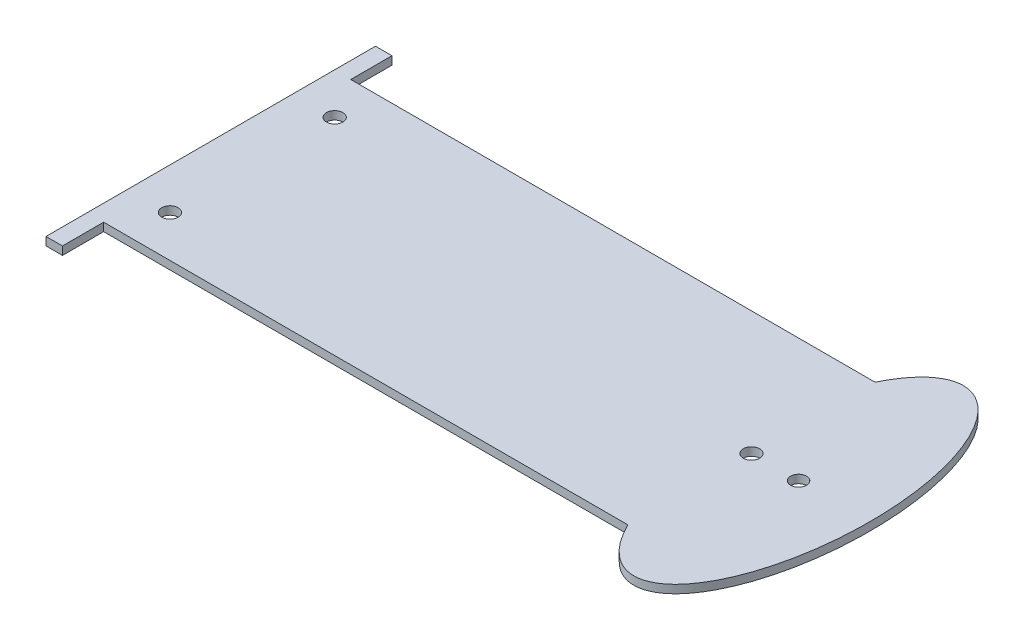
SolidWorks part; units mm, degrees
ref_plane "Front Plane" through (0, 0, 0) normal (0, 0, 1) x (1, 0, 0)
ref_plane "Top Plane" through (0, 0, 0) normal (0, 1, 0) x (1, 0, 0)
ref_plane "Right Plane" through (0, 0, 0) normal (1, 0, 0) x (0, 0, -1)
sketch "Sketch1" plane through (0, 0, 0) normal (0, 1, 0) x (1, 0, 0)
  line L0 (107.6735, 26.1875) -> (108.6754, 26.1875)
  line L1 (-83.0207, 26.1875) -> (78.6319, 26.1875)
  line L2 (-88.1007, 26.1875) -> (-88.1007, -50.0125)
  line L3 (-83.0207, -50.0125) -> (78.6272, -50.0125)
  line L6 (-88.1007, 26.1875) -> (-88.1007, 38.8875)
  line L7 (-88.1007, 38.8875) -> (-83.0207, 38.8875)
  line L8 (-83.0207, 26.1875) -> (-83.0207, 38.8875)
  line L10 (-88.1007, -50.0125) -> (-88.1007, -62.7125)
  line L11 (-88.1007, -62.7125) -> (-83.0207, -62.7125)
  line L12 (-83.0207, -50.0125) -> (-83.0207, -62.7125)
  ellipse E0 centre (93.1491, -11.91) end of major axis (93.1549, 38.8925) minor radius 21.9502 (78.6272, -50.0125) -> (78.6319, 26.1875) ccw
  dimension "D3" = 5.08
  dimension "D4" = 12.7
  dimension "D5" = 5.08
  dimension "D6" = 12.7
extrude "Boss-Extrude1" add sketch "Sketch1" along normal blind 2.54 contours L3 E0 L1 L8 L7 L6 L2 L10 L11 L12
sketch "Sketch2" plane through (0, 2.54, 0) normal (0, 1, 0) x (1, 0, 0)
  line L0 (-83.0207, 26.1875) -> (-75.4035, 26.1875)
  line L1 (-83.0207, 26.1875) -> (78.6319, 26.1875) construction
  circle A0 centre (-75.4035, 13.6003) radius 2.54
  circle A1 centre (-75.4035, -37.2013) radius 2.54
  circle A2 centre (78.6295, -11.9125) radius 2.54
  circle A3 centre (93.1491, -11.91) radius 2.4473
  dimension "D1" = 5.08
  dimension "D2" = 5.08
  dimension "D3" = 5.08
  dimension "D4" = 14.5196
extrude "Cut-Extrude1" cut sketch "Sketch2" against normal blind 2.54 contours A0 | A1 | A2 | A3
